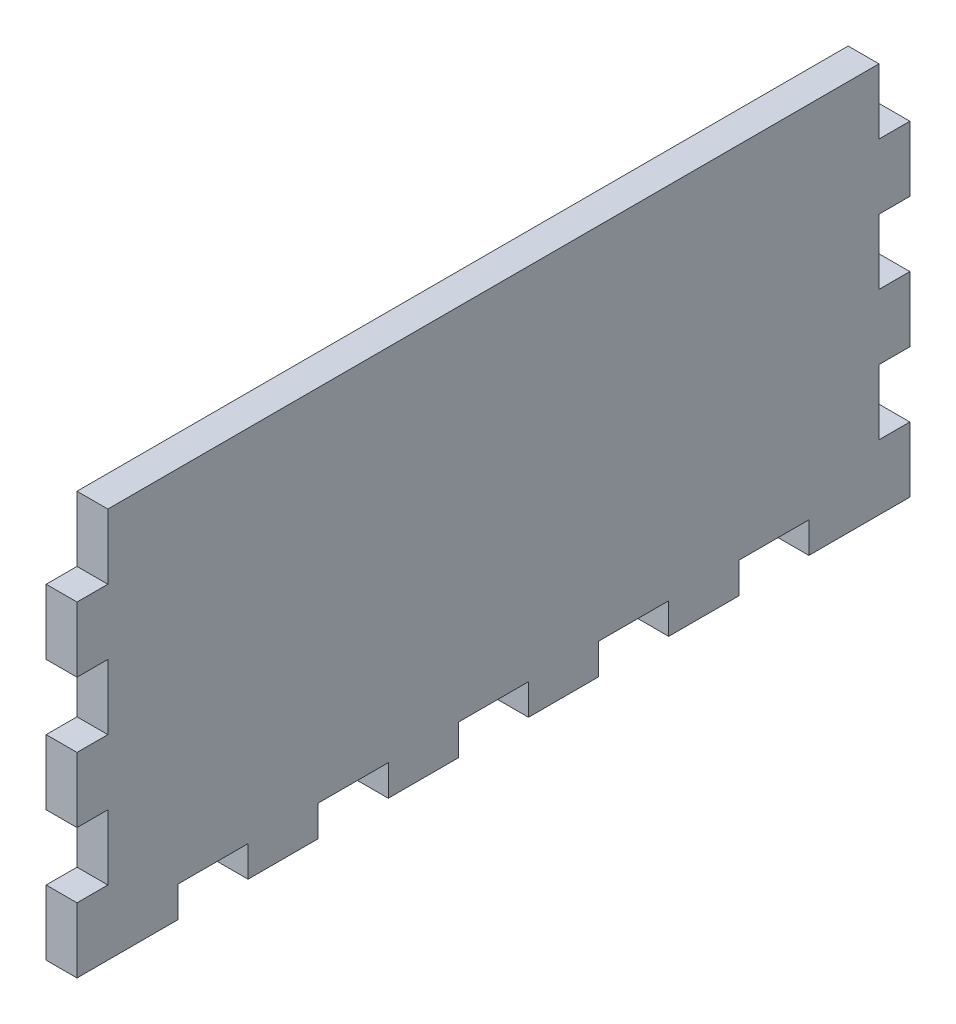
SolidWorks part; units mm, degrees
material "Pino"
ref_plane "Piano frontale" through (0, 0, 0) normal (0, 0, 1) x (1, 0, 0)
ref_plane "Piano superiore" through (0, 0, 0) normal (0, 1, 0) x (1, 0, 0)
ref_plane "Piano destro" through (0, 0, 0) normal (1, 0, 0) x (0, 0, -1)
sketch "Schizzo1" plane through (0, 0, 0) normal (1, 0, 0) x (0, 0, -1)
  line L0 (-40.5, -20.5) -> (-37.5, -20.5)
  line L1 (-37.5, 17.5) -> (37.5, 17.5)
  line L2 (-37.5, 17.5) -> (-37.5, -17.5) construction
  line L3 (-37.5, -17.5) -> (37.5, -17.5) construction
  line L4 (37.5, 17.5) -> (37.5, -17.5) construction
  line L5 (-37.5, 17.5) -> (37.5, -17.5) construction
  line L6 (-37.5, -17.5) -> (37.5, 17.5) construction
  line L7 (0, 17.5) -> (0, -17.5) construction
  line L8 (-37.5, 17.5) -> (-37.5, 11.1667)
  line L9 (-37.5, 11.1667) -> (-40.5, 11.1667)
  line L10 (-37.5, -20.5) -> (-30.6818, -20.5)
  line L11 (-40.5, 11.1667) -> (-40.5, 4.8333)
  line L12 (-40.5, 4.8333) -> (-37.5, 4.8333)
  line L13 (40.5, -14.1667) -> (40.5, -20.5)
  line L14 (30.6818, -20.5) -> (37.5, -20.5)
  line L15 (-37.5, 4.8333) -> (-37.5, -1.5)
  line L16 (-37.5, -1.5) -> (-40.5, -1.5)
  line L17 (-40.5, -1.5) -> (-40.5, -7.8333)
  line L18 (-40.5, -7.8333) -> (-37.5, -7.8333)
  line L19 (-37.5, -7.8333) -> (-37.5, -14.1667)
  line L20 (-37.5, -14.1667) -> (-40.5, -14.1667)
  line L21 (-40.5, -14.1667) -> (-40.5, -20.5)
  line L22 (37.5, -14.1667) -> (40.5, -14.1667)
  line L23 (37.5, -20.5) -> (40.5, -20.5)
  line L24 (37.5, -7.8333) -> (37.5, -14.1667)
  line L25 (40.5, -7.8333) -> (37.5, -7.8333)
  line L26 (40.5, -1.5) -> (40.5, -7.8333)
  line L27 (37.5, -1.5) -> (40.5, -1.5)
  line L28 (37.5, 4.8333) -> (37.5, -1.5)
  line L29 (40.5, 4.8333) -> (37.5, 4.8333)
  line L30 (40.5, 11.1667) -> (40.5, 4.8333)
  line L31 (37.5, 11.1667) -> (40.5, 11.1667)
  line L32 (37.5, 17.5) -> (37.5, 11.1667)
  line L34 (-30.6818, -20.5) -> (-30.6818, -17.5)
  line L35 (-30.6818, -17.5) -> (-23.8636, -17.5)
  line L36 (-23.8636, -17.5) -> (-23.8636, -20.5)
  line L37 (-23.8636, -20.5) -> (-17.0455, -20.5)
  line L38 (-17.0455, -20.5) -> (-17.0455, -17.5)
  line L39 (-17.0455, -17.5) -> (-10.2273, -17.5)
  line L40 (-10.2273, -17.5) -> (-10.2273, -20.5)
  line L41 (-10.2273, -20.5) -> (-3.4091, -20.5)
  line L42 (-3.4091, -20.5) -> (-3.4091, -17.5)
  line L43 (-3.4091, -17.5) -> (3.4091, -17.5)
  line L44 (3.4091, -17.5) -> (3.4091, -20.5)
  line L45 (3.4091, -20.5) -> (10.2273, -20.5)
  line L46 (10.2273, -20.5) -> (10.2273, -17.5)
  line L47 (10.2273, -17.5) -> (17.0455, -17.5)
  line L48 (17.0455, -17.5) -> (17.0455, -20.5)
  line L49 (17.0455, -20.5) -> (23.8636, -20.5)
  line L50 (23.8636, -20.5) -> (23.8636, -17.5)
  line L51 (23.8636, -17.5) -> (30.6818, -17.5)
  line L52 (30.6818, -17.5) -> (30.6818, -20.5)
  point P0 (0, 0)
  dimension "D1" = 35
  dimension "D2" = 75
  dimension "D3" = 3
extrude "Estrusione-Estrusione3" add sketch "Schizzo1" along normal mid plane 3
